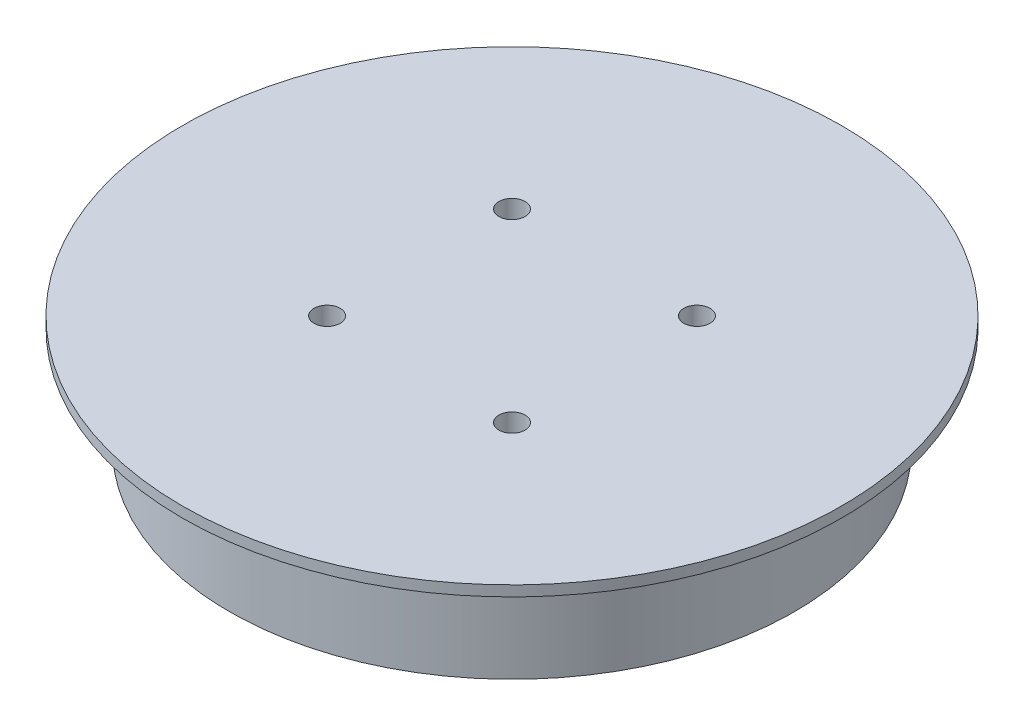
SolidWorks part; units mm, degrees
ref_plane "Front Plane" through (0, 0, 0) normal (0, 0, 1) x (1, 0, 0)
ref_plane "Top Plane" through (0, 0, 0) normal (0, 1, 0) x (1, 0, 0)
ref_plane "Right Plane" through (0, 0, 0) normal (1, 0, 0) x (0, 0, -1)
sketch "Sketch1" plane through (0, 0, 0) normal (0, 1, 0) x (1, 0, 0)
  circle A0 centre (0, 0) radius 31.5
extrude "Boss-Extrude1" add sketch "Sketch1" along normal blind 11
hole_wizard "Tap Drill for M3x0.5 Tap1" positions "Sketch3" profile "Sketch2" hole size "M3x0.5" standard "ANSI Metric"
sketch "Sketch3" plane through (0, 11, 0) normal (0, 1, 0) x (1, 0, 0)
  line L0 (0, 0) -> (-8.8388, 8.8388) construction
  line L2 (0, 0) -> (8.8388, 8.8388) construction
  line L4 (0, 0) -> (8.8388, -8.8388) construction
  line L6 (0, 0) -> (-8.8388, -8.8388) construction
  point P2 (-8.8388, 8.8388)
  point P8 (8.8388, 8.8388)
  point P13 (8.8388, -8.8388)
  point P17 (-8.8388, -8.8388)
sketch "Sketch2" plane through (-8.8388, 11, -8.8388) normal (1, 0, 0) x (0, 0, 1)
  line L0 (0, 0) -> (0, 7.7511)
  line L1 (0, 7.7511) -> (1.25, 7)
  line L2 (1.25, 7) -> (1.25, 0)
  line L5 (1.25, 0) -> (0, 0)
  line L10 (0, 7.7511) -> (-1.25, 7) construction
  line L11 (0, -6.35) -> (0, 107.95) construction
  dimension "Hole Dia." = 2.5
  dimension "Hole Depth" = 7
  dimension "Drill Angle" = 118
sketch "Sketch9" plane through (0, 0, 0) normal (0, -1, 0) x (1, 0, 0)
  circle A0 centre (0, 0) radius 27
extrude "Cut-Extrude1" cut sketch "Sketch9" against normal blind 10 flip side to cut
